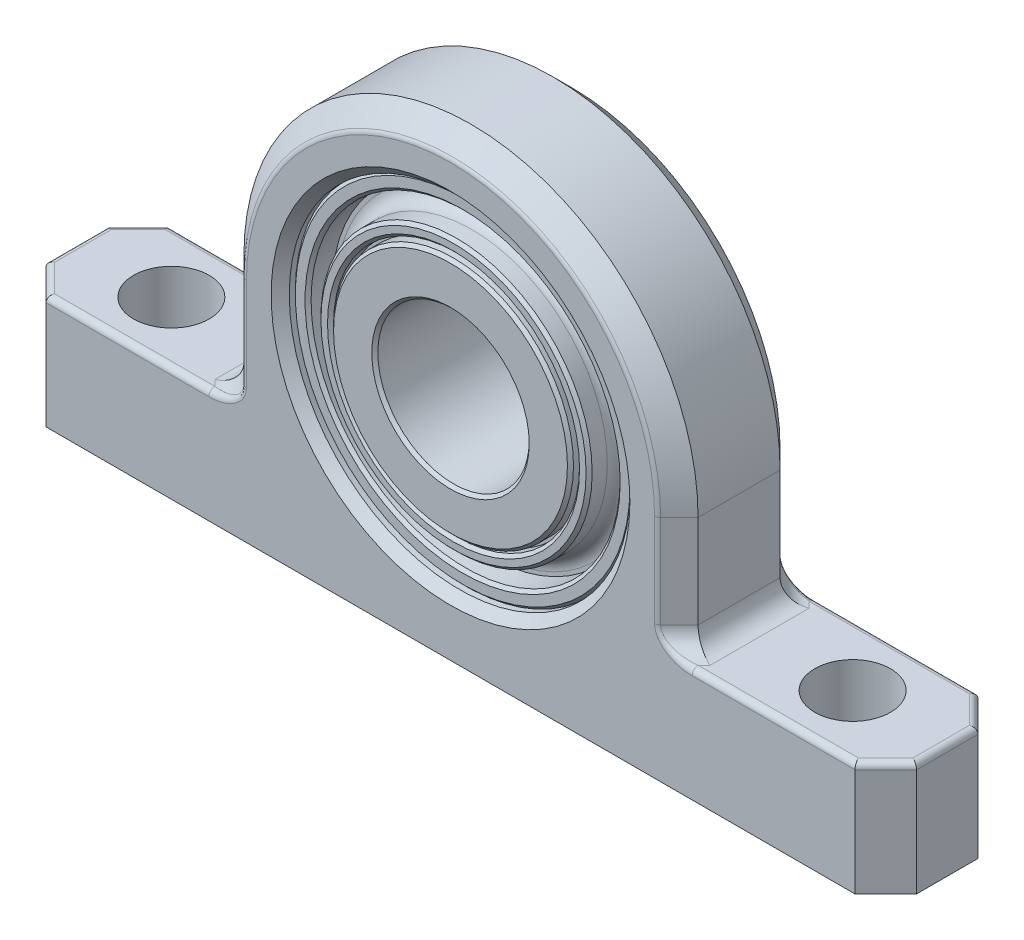
SolidWorks part; units mm, degrees
ref_plane "Front Plane" through (0, 0, 0) normal (0, 0, 1) x (1, 0, 0)
ref_plane "Top Plane" through (0, 0, 0) normal (0, 1, 0) x (1, 0, 0)
ref_plane "Right Plane" through (0, 0, 0) normal (1, 0, 0) x (0, 0, -1)
sketch "Sketch1" plane through (0, 0, 0) normal (0, 0, 1) x (1, 0, 0)
  line L0 (9.525, 0) -> (9.525, -4.7625)
  line L1 (9.525, -4.7625) -> (18.2562, -4.7625)
  line L2 (18.2562, -4.7625) -> (18.2562, -9.525)
  line L3 (18.2562, -9.525) -> (-18.2563, -9.525)
  line L4 (-18.2563, -9.525) -> (-18.2563, -4.7625)
  line L5 (-18.2563, -4.7625) -> (-9.525, -4.7625)
  line L6 (-9.525, -4.7625) -> (-9.525, 0)
  circle A0 centre (0, 0) radius 3.175
  arc A1 (9.525, 0) -> (-9.525, 0) centre (0, 0) ccw
  circle A2 centre (0, 0) radius 7.1438
  point P12 (0, 7.1437)
  point P13 (0, 3.175)
  dimension "shaft dia" = 6.35
  dimension "D1" = 14.2875
sketch "Sketch2" plane through (0, 0, 0) normal (0, 1, 0) x (1, 0, 0)
  line L0 (0, 2.5797) -> (0, -2.5797) construction
  line L1 (-14.2875, 0) -> (14.2875, 0) construction
  circle A0 centre (14.2875, 0) radius 1.5875
  circle A1 centre (-14.2875, 0) radius 1.5875
  dimension "Overall Width" = 5.1594
sketch "Sketch3" plane through (0, 0, 0) normal (0, 0, 1) x (1, 0, 0)
  line L0 (9.525, 0) -> (9.525, -4.7625) construction
  line L1 (18.2562, -4.7625) -> (18.2562, -9.525) construction
  line L2 (9.525, -4.7625) -> (18.2562, -4.7625) construction
  line L3 (18.2562, -9.525) -> (-18.2563, -9.525) construction
  line L4 (-18.2563, -9.525) -> (-18.2563, -4.7625) construction
  line L5 (-18.2563, -4.7625) -> (-9.525, -4.7625) construction
  line L6 (-9.525, -4.7625) -> (-9.525, 0) construction
  line L7 (9.525, 0) -> (9.525, -4.7625)
  line L8 (18.2562, -4.7625) -> (18.2562, -9.525)
  line L9 (9.525, -4.7625) -> (18.2562, -4.7625)
  line L10 (18.2562, -9.525) -> (-18.2563, -9.525)
  line L11 (-18.2563, -9.525) -> (-18.2563, -4.7625)
  line L12 (-18.2563, -4.7625) -> (-9.525, -4.7625)
  line L13 (-9.525, -4.7625) -> (-9.525, 0)
  arc A0 (9.525, 0) -> (-9.525, 0) centre (0, 0) ccw construction
  circle A1 centre (0, 0) radius 7.1438 construction
  arc A2 (9.525, 0) -> (-9.525, 0) centre (0, 0) ccw
  circle A3 centre (0, 0) radius 7.1438
extrude "Extrude1" add sketch "Sketch3" along normal up to vertex (2.5797 mm away) and the other way up to vertex (2.5797 mm away) up to point (0, 0, 2.5797) other way up to point (0, 0, -2.5797)
sketch "Sketch4" plane through (0, -4.7625, 0) normal (0, 1, 0) x (1, 0, 0)
  line L0 (-18.2563, 2.5797) -> (-18.2563, 1.2898)
  line L1 (-18.2563, -2.5797) -> (-18.2563, 2.5797) construction
  line L2 (-18.2563, 1.2898) -> (-16.9664, 2.5797)
  line L3 (-9.525, 2.5797) -> (-18.2563, 2.5797) construction
  line L4 (-16.9664, 2.5797) -> (-18.2563, 2.5797)
  line L5 (0, 0) -> (0, 2.5797) construction
  line L6 (0, 0) -> (-14.2875, 0) construction
  line L7 (16.9664, 2.5797) -> (18.2563, 2.5797)
  line L8 (18.2563, 1.2898) -> (16.9664, 2.5797)
  line L9 (18.2563, 2.5797) -> (18.2563, 1.2898)
  line L10 (18.2563, -2.5797) -> (18.2563, -1.2898)
  line L11 (18.2563, -1.2898) -> (16.9664, -2.5797)
  line L12 (16.9664, -2.5797) -> (18.2563, -2.5797)
  line L13 (-16.9664, -2.5797) -> (-18.2563, -2.5797)
  line L14 (-18.2563, -1.2898) -> (-16.9664, -2.5797)
  line L15 (-18.2563, -2.5797) -> (-18.2563, -1.2898)
  circle A0 centre (-14.2875, 0) radius 1.5875 construction
  circle A1 centre (14.2875, 0) radius 1.5875 construction
  circle A2 centre (-14.2875, 0) radius 1.5875
  circle A3 centre (14.2875, 0) radius 1.5875
  dimension "D1" = 45
  dimension "D2" = 1.2898
extrude "Cut-Extrude1" cut sketch "Sketch4" against normal through all
chamfer "Chamfer3" distance 0.8599 angle 45 6 edges at (-9.525, -2.3812, -2.5797) (0, 9.525, -2.5797) (9.525, -2.3812, -2.5797) (-9.525, -2.3812, 2.5797) (0, 9.525, 2.5797) (9.525, -2.3812, 2.5797)
fillet "Fillet6" radius 0.8599 6 edges at (9.525, -4.7625, 0) (9.0951, -4.7625, -2.1497) (9.0951, -4.7625, 2.1497) (-9.0951, -4.7625, -2.1497) (-9.0951, -4.7625, 2.1497) (-9.525, -4.7625, 0)
fillet "Fillet7" radius 0.254 20 edges at (13.4238, -4.7625, -2.5797) (9.0213, -4.5106, -2.5797) (8.6651, -1.9513, -2.5797) (0, 8.6651, -2.5797) (-8.6651, -1.9513, -2.5797) (-9.0213, -4.5106, -2.5797) (13.4238, -4.7625, 2.5797) (9.0213, -4.5106, 2.5797) (8.6651, -1.9513, 2.5797) (0, 8.6651, 2.5797) (-8.6651, -1.9513, 2.5797) (-9.0213, -4.5106, 2.5797) (17.6113, -4.7625, 1.9348) (18.2562, -4.7625, 0) (17.6113, -4.7625, -1.9348) (-13.4238, -4.7625, -2.5797) (-17.6113, -4.7625, -1.9348) (-18.2563, -4.7625, 0) (-17.6113, -4.7625, 1.9348) (-13.4238, -4.7625, 2.5797)
chamfer "Chamfer4" distance 0.381 angle 45 2 edges at (7.1438, 0, -2.5797) (7.1438, 0, 2.5797)
sketch "Sketch5" plane through (0, 0, 0) normal (1, 0, 0) x (0, 0, -1)
  line L0 (-2.0717, 6.4823) -> (-1.0557, 6.4823)
  line L1 (0, 7.1437) -> (0, 3.175) construction
  line L2 (2.0717, 7.1437) -> (2.0717, 6.4823)
  line L4 (2.0717, 6.4823) -> (1.0557, 6.4823)
  line L5 (-1.0557, 6.4823) -> (-1.0557, 5.6885)
  line L6 (-1.0557, 5.6885) -> (-2.4527, 5.6885)
  line L7 (-1.9447, 5.0324) -> (-1.9447, 5.1594)
  line L8 (-2.5797, 3.175) -> (2.5797, 3.175)
  line L9 (-1.9447, 5.0324) -> (-2.5797, 5.0324)
  line L10 (-2.0717, 7.1437) -> (2.0717, 7.1437)
  line L11 (1.0557, 6.4823) -> (1.0557, 5.6885)
  line L12 (-2.5797, 5.0324) -> (-2.5797, 3.175)
  line L13 (-2.0717, 7.1437) -> (-2.0717, 6.4823)
  line L15 (-1.9447, 5.1594) -> (-2.4527, 5.1594)
  line L16 (-2.4527, 5.1594) -> (-2.4527, 5.6885)
  line L17 (0, 7.1437) -> (0, 9.525) construction
  line L18 (0, 9.525) -> (0, 0) construction
  line L19 (1.0557, 5.6885) -> (2.4527, 5.6885)
  line L20 (2.4527, 5.1594) -> (2.4527, 5.6885)
  line L21 (1.9447, 5.1594) -> (2.4527, 5.1594)
  line L22 (1.9447, 5.0324) -> (1.9447, 5.1594)
  line L23 (1.9447, 5.0324) -> (2.5797, 5.0324)
  line L24 (2.5797, 5.0324) -> (2.5797, 3.175)
  line L27 (1.7198, 9.525) -> (-1.7198, 9.525) construction
  point P9 (0, 5.1594)
  dimension "D1" = 3.9688
  dimension "D2" = 0.6615
  dimension "D3" = 0.7938
  dimension "D6" = 1.016
  dimension "D5" = 0.635
  dimension "D7" = 0.127
  dimension "D8" = 0.127
  dimension "D9" = 0.508
revolve "Revolve1" add sketch "Sketch5" angle 360 about L0
chamfer "Chamfer5" distance 0.127 angle 45 12 edges at (-5.0324, 0, 2.5797) (-3.175, 0, 2.5797) (-5.6885, 0, 2.4527) (-5.1594, 0, 2.4527) (-7.1437, 0, 2.0717) (-6.4823, 0, 2.0717) (-3.175, 0, -2.5797) (-5.0324, 0, -2.5797) (-5.1594, 0, -2.4527) (-5.6885, 0, -2.4527) (-6.4823, 0, -2.0717) (-7.1437, 0, -2.0717)
fillet "Fillet8" radius 0.635 2 edges at (-5.6885, 0, 1.0557) (-5.6885, 0, -1.0557)
equation "\"D1@Sketch1\"=\"I@Sketch1\"*.75"
equation "\"D2@Sketch4\" = \"Overall Width@Sketch2\" / 4"
equation "\"D1@Chamfer3\" = \"Overall Width@Sketch2\" / 6"
equation "\"D1@Fillet6\"=\"D1@Chamfer3\""
equation "\"D2@Sketch5\"=\"D1@Sketch5\"/6"
equation "\"D3@Sketch5\"=\"D2@Sketch5\"*1.2"
